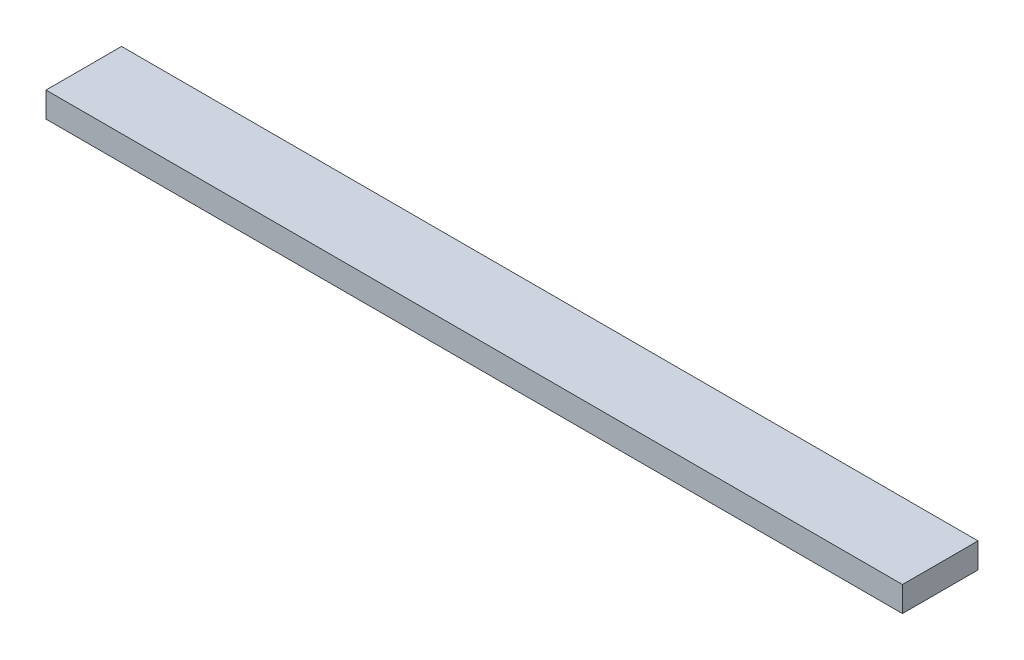
SolidWorks part; units mm, degrees
material "Acrílico (Impacto medio-alto)"
ref_plane "Alzado" through (0, 0, 0) normal (0, 0, 1) x (1, 0, 0)
ref_plane "Planta" through (0, 0, 0) normal (0, 1, 0) x (1, 0, 0)
ref_plane "Vista lateral" through (0, 0, 0) normal (1, 0, 0) x (0, 0, -1)
sketch "Croquis1" plane through (0, 0, 0) normal (0, 1, 0) x (1, 0, 0)
  line L1 (0, 0) -> (170, 0)
  line L2 (0, 0) -> (0, 15)
  line L3 (0, 15) -> (170, 15)
  line L4 (170, 0) -> (170, 15)
  dimension "D1" = 15
  dimension "D2" = 170
extrude "Saliente-Extruir1" add sketch "Croquis1" along normal blind 5
